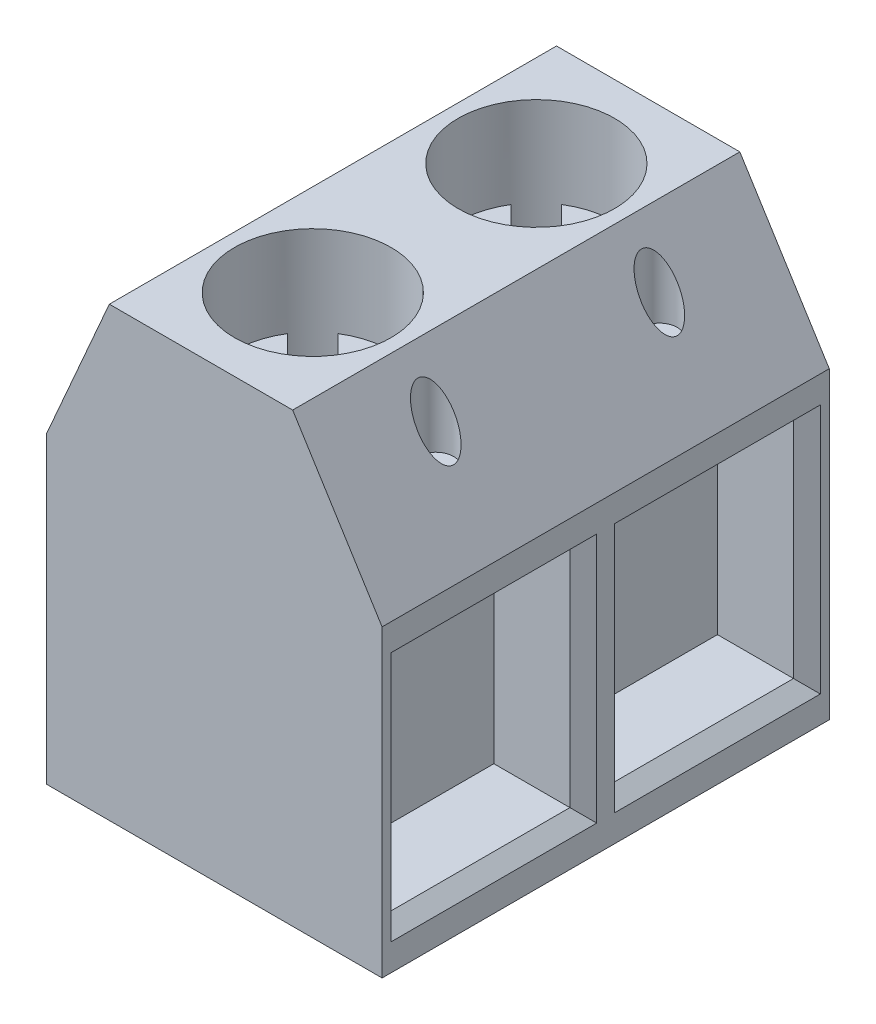
SolidWorks part; units mm, degrees
ref_plane "Front Plane" through (0, 0, 0) normal (0, 0, 1) x (1, 0, 0)
ref_plane "Top Plane" through (0, 0, 0) normal (0, 1, 0) x (1, 0, 0)
ref_plane "Right Plane" through (0, 0, 0) normal (1, 0, 0) x (0, 0, -1)
sketch "Sketch1" plane through (0, 0, 0) normal (0, 0, 1) x (1, 0, 0)
  line L0 (-3.75, 0) -> (3.75, 0)
  line L1 (3.75, 0) -> (3.75, 6.8)
  line L2 (3.75, 6.8) -> (1.75, 10)
  line L3 (1.75, 10) -> (-2.35, 10)
  line L4 (-3.75, 0) -> (-3.75, 6.8)
  line L5 (-2.35, 10) -> (-3.75, 6.8)
  dimension "D1" = 1.4
  dimension "D2" = 7.5
  dimension "D3" = 10
  dimension "D4" = 2
  dimension "D5" = 6.8
extrude "Boss-Extrude1" add sketch "Sketch1" along normal mid plane 10
sketch "Sketch2" plane through (0, 0, 0) normal (0, -1, 0) x (1, 0, 0)
  line L0 (0.45, 2) -> (0.45, -2.5) construction
  line L1 (-0.05, 3) -> (0.95, 3)
  line L2 (-0.05, 3) -> (-0.05, 2)
  line L3 (-0.05, 2) -> (0.95, 2)
  line L4 (0.95, 3) -> (0.95, 2)
  line L5 (-0.05, -2) -> (0.95, -2)
  line L6 (-0.05, -2) -> (-0.05, -3)
  line L7 (-0.05, -3) -> (0.95, -3)
  line L8 (0.95, -2) -> (0.95, -3)
  line L14 (0.95, 2.5) -> (3.5135, 2.5) construction
  line L15 (0.95, -2.5) -> (0, -2.5) construction
  line L17 (0.95, -3) -> (-0.05, -2) construction
  line L18 (3.75, 5) -> (3.75, -5) construction
  dimension "D1" = 5
  dimension "D2" = 2.5
  dimension "D3" = 1
  dimension "D4" = 3.3
extrude "Boss-Extrude2" add sketch "Sketch2" along normal blind 1
sketch "Sketch3" plane through (3.75, 0, 0) normal (1, 0, 0) x (0, 0, -1)
  line L0 (2.5, 0.9) -> (2.5, -1) construction
  line L1 (-4.5, 5.9) -> (-0.5, 5.9)
  line L2 (-4.5, 5.9) -> (-4.5, 0.9)
  line L3 (-4.5, 0.9) -> (-0.5, 0.9)
  line L4 (-0.5, 5.9) -> (-0.5, 0.9)
  line L5 (3, -1) -> (2, -1) construction
  line L9 (0.5, 5.9) -> (4.5, 5.9)
  line L10 (0.5, 5.9) -> (0.5, 0.9)
  line L11 (0.5, 0.9) -> (4.5, 0.9)
  line L12 (4.5, 5.9) -> (4.5, 0.9)
  line L14 (-2.5, 0.9) -> (-2.5, -1) construction
  line L15 (-2, -1) -> (-3, -1) construction
  line L16 (0, 0.9) -> (0, 0) construction
  line L17 (-5, 0) -> (5, 0) construction
  dimension "D1" = 4
  dimension "D2" = 5
  dimension "D3" = 0.9
extrude "Cut-Extrude1" cut sketch "Sketch3" against normal blind 2
sketch "Sketch4" plane through (0, 10, 0) normal (0, 1, 0) x (1, 0, 0)
  line L0 (-0.3, 2.5) -> (-0.3, 0) construction
  line L1 (-0.3, 0) -> (-0.3, -2.5) construction
  line L2 (-0.3, 0) -> (0, 0) construction
  line L3 (-0.3, 2.5) -> (-0.3, 5) construction
  line L4 (1.75, 5) -> (-2.35, 5) construction
  line L5 (2.45, 2.5) -> (-3.05, 2.5) construction
  line L6 (2.45, -2.5) -> (-3.05, -2.5) construction
  line L7 (-3.05, 2.5) -> (-3.05, -2.5) construction
  circle A0 centre (-0.3, 2.5) radius 1.75
  circle A2 centre (-0.3, -2.5) radius 1.75
  circle A3 centre (2.45, 2.5) radius 0.4
  circle A4 centre (2.45, -2.5) radius 0.4
  circle A5 centre (-3.05, 2.5) radius 0.4
  circle A6 centre (-3.05, -2.5) radius 0.4
  dimension "D1" = 3.5
  dimension "D3" = 2.5
  dimension "D4" = 0.8
  dimension "D8" = 2.75
  dimension "D2" = 2.5
  dimension "D5" = 5
  dimension "D6" = 2.5
  dimension "D7" = 5.5
extrude "Cut-Extrude2" cut sketch "Sketch4" against normal blind 2
sketch "Sketch5" plane through (0, 8, 0) normal (0, 1, 0) x (1, 0, 0)
  line L0 (-0.3, 2.5) -> (-1.5374, 3.7374) construction
  line L1 (-1.2218, -1.0125) -> (-0.3, -1.9343)
  line L2 (-0.3, -1.9343) -> (0.1243, -1.5101)
  line L3 (-0.3, 2.5) -> (0.4071, 3.2071) construction
  line L4 (-1.2218, 3.9875) -> (-0.3, 3.0657)
  line L5 (0.6218, 1.0125) -> (-0.3, 1.9343)
  line L6 (0.1243, -1.5101) -> (0.6899, -2.0757)
  line L7 (0.6899, -2.0757) -> (0.2657, -2.5)
  line L8 (0.2657, -2.5) -> (1.1875, -3.4218)
  line L9 (0.6218, -3.9875) -> (-0.3, -3.0657)
  line L10 (-3.75, -5) -> (-3.75, 5) construction
  line L11 (-0.3, 3.0657) -> (0.1243, 3.4899)
  line L12 (0.1243, 3.4899) -> (0.6899, 2.9243)
  line L13 (0.6899, 2.9243) -> (0.2657, 2.5)
  line L14 (-0.3, 1.9343) -> (-0.7243, 1.5101)
  line L15 (-0.7243, 1.5101) -> (-1.2899, 2.0757)
  line L16 (-1.2899, 2.0757) -> (-0.8657, 2.5)
  line L17 (0.2657, 2.5) -> (1.1875, 1.5782)
  line L18 (-0.8657, 2.5) -> (-1.7875, 3.4218)
  line L19 (-0.3, -3.0657) -> (-0.7243, -3.4899)
  line L20 (-0.7243, -3.4899) -> (-1.2899, -2.9243)
  line L21 (-1.2899, -2.9243) -> (-0.8657, -2.5)
  line L22 (-0.8657, -2.5) -> (-1.7875, -1.5782)
  line L23 (-1.2218, -6.0125) -> (-0.3, -6.9343)
  line L24 (-0.3, -6.9343) -> (0.1243, -6.5101)
  line L25 (0.1243, -6.5101) -> (0.6899, -7.0757)
  line L26 (0.6899, -7.0757) -> (0.2657, -7.5)
  line L27 (0.2657, -7.5) -> (1.1875, -8.4218)
  line L28 (0.6218, -8.9875) -> (-0.3, -8.0657)
  line L29 (-0.3, -8.0657) -> (-0.7243, -8.4899)
  line L30 (-0.7243, -8.4899) -> (-1.2899, -7.9243)
  line L31 (-1.2899, -7.9243) -> (-0.8657, -7.5)
  line L32 (-0.8657, -7.5) -> (-1.7875, -6.5782)
  arc A0 (-1.2218, 3.9875) -> (-1.7875, 3.4218) centre (-0.3, 2.5) ccw
  circle A1 centre (-0.3, 2.5) radius 1.75 construction
  arc A2 (-1.2218, -1.0125) -> (-1.7875, -1.5782) centre (-0.3, -2.5) ccw
  arc A4 (0.6218, 1.0125) -> (1.1875, 1.5782) centre (-0.3, 2.5) ccw
  arc A5 (0.6218, -3.9875) -> (1.1875, -3.4218) centre (-0.3, -2.5) ccw
  arc A6 (-1.2218, -6.0125) -> (-1.7875, -6.5782) centre (-0.3, -7.5) ccw
  arc A7 (0.6218, -8.9875) -> (1.1875, -8.4218) centre (-0.3, -7.5) ccw
  dimension "D1" = 45
  dimension "D2" = 0.8
  dimension "D3" = 2
  dimension "D4" = 0.8
  dimension "D5" = 3
extrude "Cut-Extrude3" cut sketch "Sketch5" against normal blind 0.5
chamfer "Chamfer1" distance 0.3 angle 45 8 edges at (3.75, 3.4, 0.5) (3.75, 5.9, 2.5) (3.75, 3.4, 4.5) (3.75, 0.9, 2.5) (3.75, 3.4, -4.5) (3.75, 5.9, -2.5) (3.75, 3.4, -0.5) (3.75, 0.9, -2.5)
